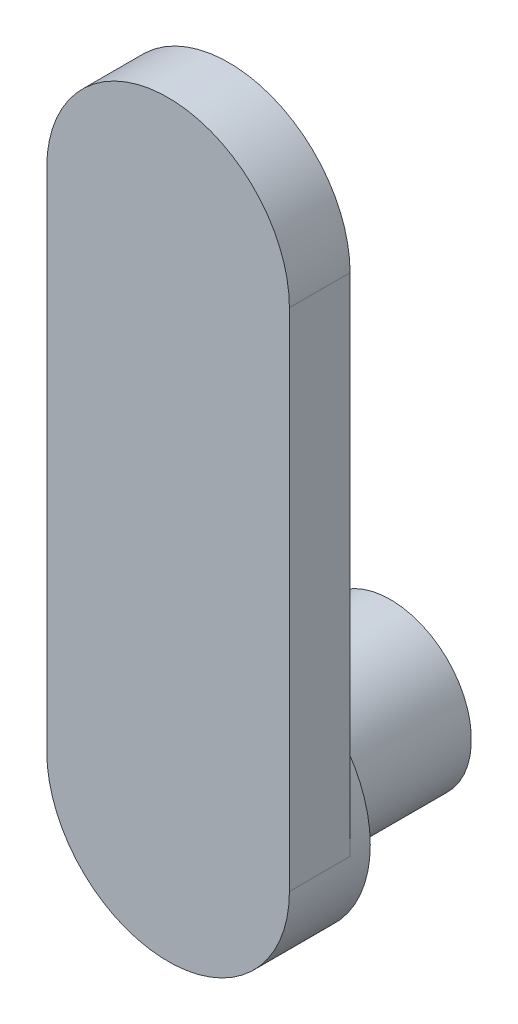
SolidWorks part; units mm, degrees
ref_plane "Front Plane" through (0, 0, 0) normal (0, 0, 1) x (1, 0, 0)
ref_plane "Top Plane" through (0, 0, 0) normal (0, 1, 0) x (1, 0, 0)
ref_plane "Right Plane" through (0, 0, 0) normal (1, 0, 0) x (0, 0, -1)
sketch "Sketch1" plane through (0, 0, 0) normal (0, 0, 1) x (1, 0, 0)
  circle A0 centre (0, 0) radius 6
  dimension "D1" = 12
extrude "Boss-Extrude1" add sketch "Sketch1" against normal blind 1
sketch "Sketch2" plane through (0, 0, 0) normal (0, 0, 1) x (1, 0, 0)
  line L0 (0, 0) -> (0, 25) construction
  line L1 (-6, 0) -> (-6, 25)
  line L2 (6, 0) -> (6, 25)
  arc A0 (-6, 0) -> (6, 0) centre (0, 0) ccw
  arc A1 (6, 25) -> (-6, 25) centre (0, 25) ccw
  point P3 (0, 12.5)
  dimension "D1" = 6
  dimension "D2" = 25
extrude "Boss-Extrude2" add sketch "Sketch2" along normal blind 3
sketch "Sketch3" plane through (0, 0, -1) normal (0, 0, -1) x (-1, 0, 0)
  circle A0 centre (0, 0) radius 4
  dimension "D1" = 8
extrude "Boss-Extrude3" add sketch "Sketch3" along normal blind 7
